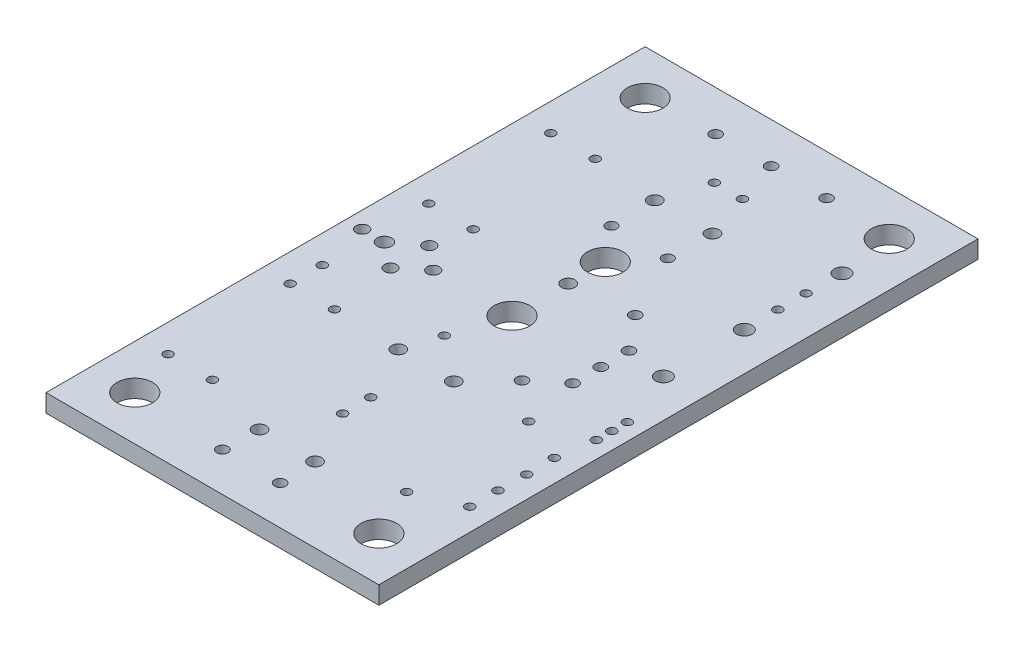
SolidWorks part; units mm, degrees
ref_plane "Plan de face" through (0, 0, 0) normal (0, 0, 1) x (1, 0, 0)
ref_plane "Plan de dessus" through (0, 0, 0) normal (0, 1, 0) x (1, 0, 0)
ref_plane "Plan de droite" through (0, 0, 0) normal (1, 0, 0) x (0, 0, -1)
sketch "Esquisse2" plane through (0, 0, 0) normal (0, 1, 0) x (1, 0, 0)
  line L1 (0, 0) -> (30, 0)
  line L2 (0, 0) -> (0, 54)
  line L3 (0, 54) -> (30, 54)
  line L4 (30, 0) -> (30, 54)
  circle A0 centre (17.6225, 42.4459) radius 0.5994
  circle A1 centre (12.4206, 42.4459) radius 0.5994
  circle A2 centre (15.0216, 32.0446) radius 0.5994
  circle A3 centre (15.0038, 35.4025) radius 1.6002
  circle A4 centre (17.5997, 3.5001) radius 0.5004
  circle A5 centre (12.4003, 3.5001) radius 0.5004
  circle A6 centre (15.0012, 50.3504) radius 0.5004
  circle A7 centre (20, 50.3504) radius 0.5004
  circle A8 centre (10, 50.3504) radius 0.5004
  circle A9 centre (12.4993, 19.2507) radius 0.5994
  circle A10 centre (12.4993, 6.7488) radius 0.5994
  circle A11 centre (17.5006, 19.2507) radius 0.5994
  circle A12 centre (17.5006, 6.7488) radius 0.5994
  circle A13 centre (20.5003, 22.4003) radius 0.5004
  circle A14 centre (20.5003, 32.6009) radius 0.5004
  circle A15 centre (12.4612, 38.4988) radius 0.4826
  circle A16 centre (17.5412, 38.4988) radius 0.4826
  circle A17 centre (16.2712, 46.4998) radius 0.3988
  circle A18 centre (13.7312, 46.4998) radius 0.3988
  circle A19 centre (15.0012, 11.7297) radius 0.3988
  circle A20 centre (15.0012, 14.2697) radius 0.3988
  circle A21 centre (1.4986, 27.0002) radius 0.5512
  circle A22 centre (7.8994, 27.0002) radius 0.5512
  circle A23 centre (5.7988, 25.2501) radius 0.5512
  circle A24 centre (5.7988, 28.7503) radius 0.5512
  circle A25 centre (3.5001, 27.0002) radius 0.6502
  circle A26 centre (4.0005, 49.9999) radius 1.6002
  circle A27 centre (25.9994, 49.9999) radius 1.6002
  circle A28 centre (4.0005, 4.0005) radius 1.6002
  circle A29 centre (15.0012, 27.0002) radius 1.6002
  circle A30 centre (25.9994, 4.0005) radius 1.6002
  circle A31 centre (22.9997, 24.4602) radius 0.5004
  circle A32 centre (22.9997, 27.0002) radius 0.5004
  circle A33 centre (22.9997, 29.5402) radius 0.5004
  circle A34 centre (28.0492, 15.2705) radius 0.3988
  circle A35 centre (28.001, 12.7305) radius 0.3988
  circle A36 centre (28.001, 10.1905) radius 0.3988
  circle A37 centre (28.001, 17.8105) radius 0.3988
  circle A38 centre (26.4998, 41.9989) radius 0.3988
  circle A39 centre (26.4998, 39.4589) radius 0.3988
  circle A40 centre (26.5608, 45.179) radius 0.701
  circle A41 centre (26.5608, 36.3804) radius 0.701
  circle A42 centre (26.5608, 29.0805) radius 0.701
  circle A43 centre (24.0005, 8.4988) radius 0.3988
  circle A44 centre (24.0005, 19.4996) radius 0.3988
  circle A45 centre (6.4999, 42.9997) radius 0.3988
  circle A46 centre (6.4999, 31.9989) radius 0.3988
  circle A47 centre (2.4994, 42.9997) radius 0.3988
  circle A48 centre (2.4994, 31.9989) radius 0.3988
  circle A49 centre (6.4999, 8.4988) radius 0.3988
  circle A50 centre (6.4999, 19.4996) radius 0.3988
  circle A51 centre (2.4994, 8.4988) radius 0.3988
  circle A52 centre (2.4994, 19.4996) radius 0.3988
  circle A53 centre (2.4994, 22.4003) radius 0.3988
  circle A54 centre (13.5001, 22.4003) radius 0.3988
  circle A55 centre (28.4988, 21.0998) radius 0.3988
  circle A56 centre (28.4988, 22.4993) radius 0.3988
  circle A57 centre (28.4988, 23.8989) radius 0.3988
extrude "Extrusion1" add sketch "Esquisse2" along normal blind 1.6
